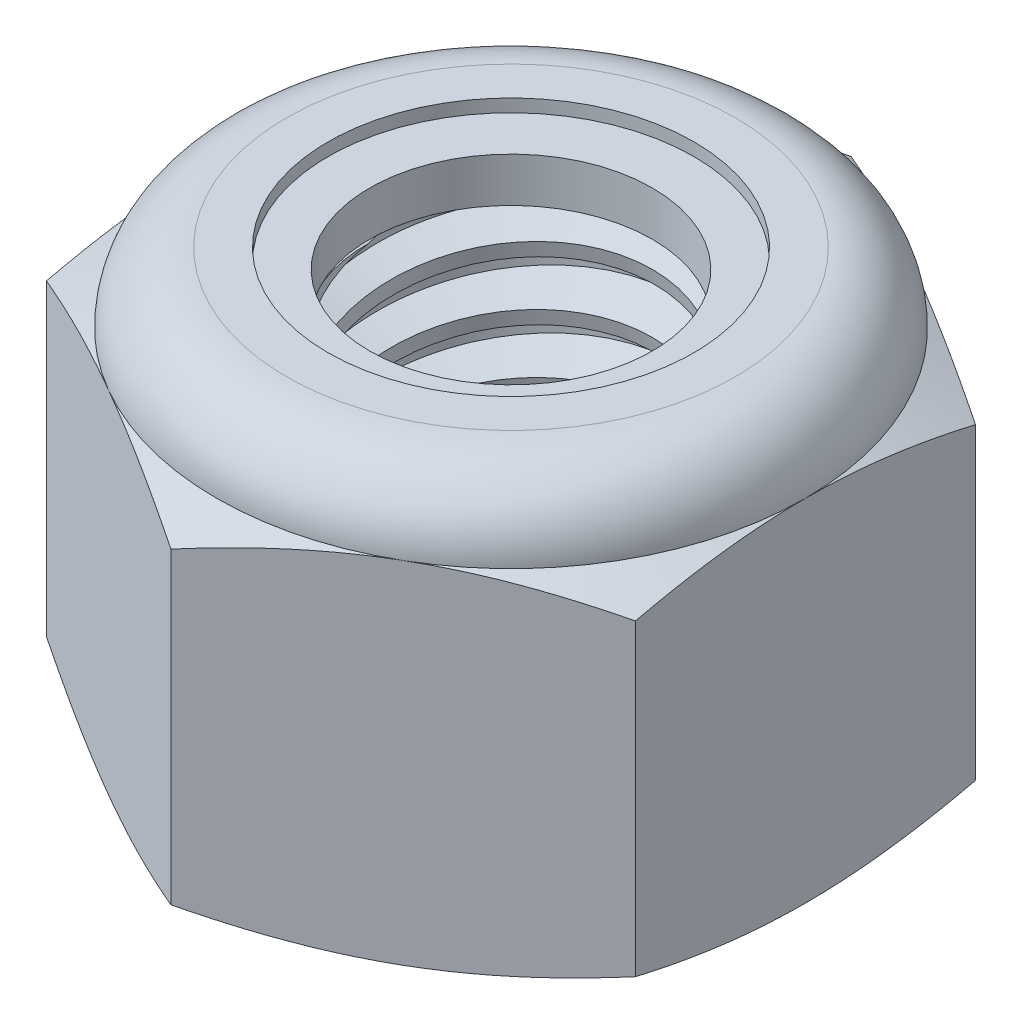
SolidWorks part; units mm, degrees
material "AISI Type 316L stainless steel"
ref_plane "Front" through (0, 0, 0) normal (0, 0, 1) x (1, 0, 0)
ref_plane "Top" through (0, 0, 0) normal (0, 1, 0) x (1, 0, 0)
ref_plane "Right" through (0, 0, 0) normal (1, 0, 0) x (0, 0, -1)
sketch "Sketch1" plane through (0, 0, 0) normal (0, 1, 0) x (1, 0, 0)
  line L1 (0, 4.0415) -> (-3.5, 2.0207)
  line L2 (-3.5, 2.0207) -> (-3.5, -2.0207)
  line L3 (-3.5, -2.0207) -> (0, -4.0415)
  line L4 (0, -4.0415) -> (3.5, -2.0207)
  line L5 (3.5, -2.0207) -> (3.5, 2.0207)
  line L6 (3.5, 2.0207) -> (0, 4.0415)
  circle A0 centre (0, 0) radius 3.5 construction
  dimension "Hex Flats" = 7
extrude "Extrude1" add sketch "Sketch1" along normal blind 5
sketch "Sketch2" plane through (0, 0, 0) normal (1, 0, 0) x (0, 0, -1)
  line L0 (-2, 0) -> (-2, 5) construction
  line L1 (0, 0) -> (2, 0)
  line L2 (0, 0) -> (0, 5)
  line L3 (0, 5) -> (2, 5)
  line L4 (2, 0) -> (2, 5)
  line L5 (-2.0207, 5) -> (2.0207, 5) construction
  line L7 (0, -2) -> (0, 0) construction
  dimension "Thread Dia" = 4
revolve "Revolve1" add sketch "Sketch2" angle 360 about L7
sketch "Sketch3" plane through (0, 0, 0) normal (1, 0, 0) x (0, 0, -1)
  line L0 (2, 5) -> (-2, 5) construction
  line L1 (-2, 5) -> (-2, 4.3) construction
  line L2 (-2, 4.3) -> (2, 5) construction
  line L3 (2, 5) -> (2.0151, 4.9138) construction
  line L4 (2.0151, 4.9138) -> (2.1207, 4.3105)
  line L5 (2.1207, 4.3105) -> (1.7097, 4.4606)
  line L6 (1.7097, 4.4606) -> (1.6796, 4.633)
  line L7 (1.6796, 4.633) -> (2.0151, 4.9138)
  line L8 (1.6947, 4.5468) -> (2.0679, 4.6121) construction
  line L9 (2, 5) -> (2, 4.6003) construction
  line L10 (2, 4.6003) -> (-2, 3.9003) construction
  line L11 (-2, 3.9003) -> (-2, 4.3) construction
  line L12 (-0.1312, 5) -> (0.1312, 3.5005) construction
  line L13 (-2, 0) -> (-2, 5) construction
  line L14 (0, 5) -> (2, 5) construction
  line L15 (2, 0) -> (2, 5) construction
  point P13 (0, 4.2503)
  dimension "D1" = 0.0875
  dimension "D2" = 0.175
  dimension "Thread Pitch" = 0.7
  dimension "D4" = 60
  dimension "D5" = 0.7
revolve "Cut-Revolve1" cut sketch "Sketch3" angle 360 about L12
pattern_linear "LPattern1" count 7 spacing 0.7 along (0, -1, 0) count 2 spacing 0.7 along (0, 1, 0) of "Cut-Revolve1"
sketch "Sketch4" plane through (0, 0, 0) normal (1, 0, 0) x (0, 0, -1)
  line L0 (0, 5) -> (2, 5)
  line L1 (2, 5) -> (1.6796, 4.8506)
  line L2 (1.6796, 4.8506) -> (1.6796, 0.1494)
  line L3 (1.6796, 0.1494) -> (2, 0)
  line L4 (2, 0) -> (0, 0)
  line L5 (0, 0) -> (0, 5)
  line L6 (2, 0) -> (2, 5) construction
  line L7 (0, 5) -> (2, 5) construction
  line L8 (0, 0) -> (2, 0) construction
  line L9 (0, 0) -> (0, 5) construction
  line L10 (0, 5) -> (0, 5.3535) construction
  dimension "D1" = 25
revolve "Cut-Revolve2" cut sketch "Sketch4" angle 360 about L10
combine bodies "Combine1" operation type subtract main body 112 bodies to subtract 111
sketch "Sketch5" plane through (0, 0, 0) normal (1, 0, 0) x (0, 0, -1)
  line L0 (0, 0) -> (3.5, 0)
  line L1 (3.5, 0) -> (4.0415, 0.2525)
  line L2 (4.0415, 0.2525) -> (4.0415, 3.9142)
  line L3 (4.0415, 3.9142) -> (3.5, 4.1667)
  line L4 (2.6667, 5) -> (2.6667, 6.27)
  line L5 (2.6667, 6.27) -> (5.3115, 6.27)
  line L6 (5.3115, 6.27) -> (5.3115, -1.27)
  line L7 (5.3115, -1.27) -> (0, -1.27)
  line L8 (0, -1.27) -> (0, 0)
  line L9 (3.5, 4.1667) -> (3.5, 0) construction
  line L10 (0, 0) -> (2, 0) construction
  line L13 (4.0415, 2.0833) -> (5.3115, 2.0833) construction
  line L14 (4.0415, 5) -> (4.0415, 0) construction
  line L15 (0, 0) -> (0, 6.27) construction
  line L20 (0, 6.27) -> (2.6667, 6.27) construction
  line L22 (0, 5) -> (2, 5) construction
  arc A0 (3.5, 4.1667) -> (2.6667, 5) centre (2.6667, 4.1667) ccw
  dimension "D1" = 25
  dimension "D2" = 1.27
  dimension "D3" = 5
  dimension "D4" = 0.8333
revolve "Cut-Revolve3" cut sketch "Sketch5" angle 360 about L15
sketch "Sketch6" plane through (0, 0, 0) normal (1, 0, 0) x (0, 0, -1)
  line L0 (0, 4.1667) -> (3.3476, 4.1667)
  line L1 (2.6667, 4.8476) -> (2.1731, 4.8476)
  line L2 (0, 6.27) -> (0, 4.1667)
  line L3 (2.1731, 6.27) -> (0, 6.27)
  line L4 (0, 6.27) -> (2.6667, 6.27) construction
  line L5 (0, 0) -> (0, 6.27) construction
  line L6 (0, 6.27) -> (0, 44.323) construction
  line L7 (2.1731, 4.8476) -> (2.1731, 6.27)
  line L8 (2.6667, 5) -> (2.6667, 4.8476) construction
  line L9 (2.1731, 4.8476) -> (1.6796, 4.8476) construction
  line L10 (1.6796, 4.8476) -> (1.6796, 4.8506) construction
  arc A0 (3.3476, 4.1667) -> (2.6667, 4.8476) centre (2.6667, 4.1667) ccw
  arc A1 (3.5, 4.1667) -> (2.6667, 5) centre (2.6667, 4.1667) ccw construction
  dimension "D1" = 0.1524
revolve "Cut-Revolve4" cut sketch "Sketch6" angle 360 about L6
sketch "Sketch7" plane through (0, 0, 0) normal (1, 0, 0) x (0, 0, -1)
  line L0 (1.6796, 4.2429) -> (3.2666, 4.2429)
  line L1 (2.6667, 4.7714) -> (1.6796, 4.7714)
  line L2 (1.6796, 4.7714) -> (1.6796, 4.2429)
  line L3 (1.6796, 4.2429) -> (0, 4.2429) construction
  line L4 (0, 4.2429) -> (0, 4.7714) construction
  line L5 (0, 4.7714) -> (1.6796, 4.7714) construction
  line L6 (1.6796, 4.2429) -> (1.6796, 4.1667) construction
  line L7 (0, 4.1667) -> (3.3476, 4.1667) construction
  line L8 (2.6667, 4.7714) -> (2.6667, 4.8476) construction
  arc A0 (3.2666, 4.2429) -> (2.6667, 4.7714) centre (2.6667, 4.1667) ccw
  arc A2 (3.3476, 4.1667) -> (2.6667, 4.8476) centre (2.6667, 4.1667) ccw construction
  dimension "D1" = 0.0762
revolve "Revolve2" add sketch "Sketch7" angle 360 about L4
equation "\"D1@Sketch3\"=\"Thread Pitch@Sketch3\"/8"
equation "\"D2@Sketch3\"=\"Thread Pitch@Sketch3\"/4"
equation "\"D5@Sketch3\"=\"Thread Pitch@Sketch3\""
equation "\"D4@LPattern1\"=\"Thread Pitch@Sketch3\""
equation "\"D3@LPattern1\"=\"Thread Pitch@Sketch3\""
equation "\"D1@LPattern1\"=\"Height@Extrude1\"/\"Thread Pitch@Sketch3\""
equation "\"D4@Sketch5\"=\"Height@Extrude1\"/6"
